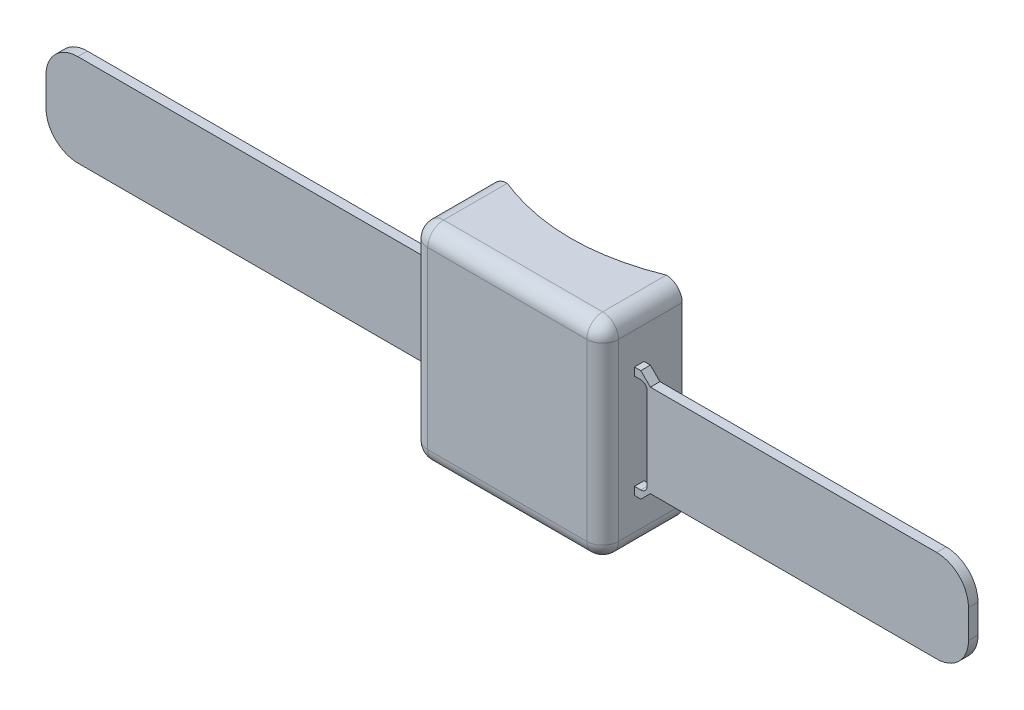
SolidWorks part; units mm, degrees
ref_plane "Alzado" through (0, 0, 0) normal (0, 0, 1) x (1, 0, 0)
ref_plane "Planta" through (0, 0, 0) normal (0, 1, 0) x (1, 0, 0)
ref_plane "Vista lateral" through (0, 0, 0) normal (1, 0, 0) x (0, 0, -1)
sketch "Croquis1" plane through (0, 0, 0) normal (0, 0, 1) x (1, 0, 0)
  line L0 (5, 0) -> (55, 0)
  line L1 (60, 5) -> (60, 60)
  line L2 (55, 65) -> (5, 65)
  line L3 (0, 60) -> (0, 5)
  arc A0 (5, 0) -> (0, 5) centre (5, 5) cw
  arc A1 (5, 65) -> (0, 60) centre (5, 60) ccw
  arc A2 (60, 60) -> (55, 65) centre (55, 60) ccw
  arc A3 (55, 0) -> (60, 5) centre (55, 5) ccw
  point P7 (0, 0)
  point P12 (60, 65)
  point P15 (60, 0)
  dimension "D1" = 65
  dimension "D3" = 5
  dimension "D2" = 60
extrude "Saliente-Extruir1" add sketch "Croquis1" against normal blind 25
fillet "Redondeo1" radius 5 8 edges at (58.5355, 63.5355, 0) (30, 65, 0) (1.4645, 63.5355, 0) (58.5355, 1.4645, 0) (1.4645, 1.4645, 0) (30, 0, 0) (0, 32.5, 0) (60, 32.5, 0)
sketch "Croquis2" plane through (0, 0, 0) normal (0, -1, 0) x (1, 0, 0)
  line L0 (5, -25) -> (55, -25)
  spline S0 degree 2 poles (5, -25) (30, -15) (55, -25) knots 0 0 0 1 1 1
  point P2 (30, -25)
  point P4 (0, 0)
  dimension "D1" = 5
extrude "Cortar-Extruir1" cut sketch "Croquis2" against normal blind 65
sketch "Croquis3" plane through (0, 0, 0) normal (-1, 0, 0) x (0, 0, 1)
  line L0 (-10, 50) -> (-10, 15)
  line L1 (-10, 15) -> (-13, 15)
  line L2 (-13, 15) -> (-13, 50)
  line L3 (-13, 50) -> (-10, 50)
  line L4 (-25, 0) -> (-5, 0) construction
  line L6 (-25, 60) -> (-25, 5) construction
  point P6 (-15, 0)
  dimension "D1" = 35
  dimension "D2" = 3
  dimension "D3" = 15
  dimension "D4" = 12
extrude "Saliente-Extruir2" add sketch "Croquis3" along normal blind 5
sketch "Croquis4" plane through (0, 0, -10) normal (0, 0, 1) x (1, 0, 0)
  line L0 (-2, 47.5) -> (0, 47.5)
  line L1 (0, 15) -> (0, 50) construction
  line L2 (0, 47.5) -> (0, 17.5)
  line L3 (0, 17.5) -> (-2, 17.5)
  line L4 (-4, 19.5) -> (-4, 45.5)
  line L5 (-5, 50) -> (0, 50) construction
  arc A0 (-2, 47.5) -> (-4, 45.5) centre (-2, 45.5) ccw
  arc A1 (-2, 17.5) -> (-4, 19.5) centre (-2, 19.5) cw
  point P5 (-1, 47.5)
  point P11 (-4, 47.5)
  point P14 (-4, 17.5)
  dimension "D4" = 2
  dimension "D1" = 30
  dimension "D2" = 4
  dimension "D3" = 2.5
extrude "Cortar-Extruir2" cut sketch "Croquis4" against normal blind 3
chamfer "Chaflán2" distance 3 angle 45 2 edges at (-5, 50, -11.5) (-5, 15, -11.5)
ref_plane "Plano1" through (30, 0, 0) normal (1, 0, 0) x (0, 0, -1)
mirror "Simetría1" about plane through (30, 0, 0) normal (1, 0, 0) of "Saliente-Extruir2"
mirror "Simetría2" about plane through (30, 0, 0) normal (1, 0, 0) of "Cortar-Extruir2"
chamfer "Chaflán3" distance 3 angle 45 2 edges at (65, 50, -11.5) (65, 15, -11.5)
ref_plane "Plano2" through (0, 0, -19.5) normal (0, 0, 1) x (1, 0, 0)
sketch "Croquis6" plane through (0, 0, -19.5) normal (0, 0, 1) x (1, 0, 0)
  line L0 (30, -13.75) -> (30, 13.75) construction
  circle A0 centre (30, 32.5) radius 9
  dimension "D1" = 18
extrude "Cortar-Extruir5" cut sketch "Croquis6" against normal blind 1.5
sketch "Croquis7" plane through (0, 0, 0) normal (0, -1, 0) x (1, 0, 0)
  line L4 (55, -25) -> (55, -5) construction
  line L5 (26, -9) -> (34, -9)
  line L6 (25, -10) -> (25, -12)
  line L7 (26, -13) -> (34, -13)
  line L8 (35, -10) -> (35, -12)
  line L10 (55, -5) -> (5, -5) construction
  arc A0 (25, -12) -> (26, -13) centre (26, -12) ccw
  arc A1 (26, -9) -> (25, -10) centre (26, -10) ccw
  arc A2 (34, -9) -> (35, -10) centre (34, -10) cw
  arc A3 (34, -13) -> (35, -12) centre (34, -12) ccw
  point P8 (25, -9)
  point P11 (35, -9)
  point P14 (35, -13)
  point P15 (35, -11)
  dimension "D3" = 1
  dimension "D1" = 10
  dimension "D2" = 4
  dimension "D4" = 20
  dimension "D5" = 4
extrude "Cortar-Extruir6" cut sketch "Croquis7" against normal blind 2.5
sketch "Croquis9" plane through (-5, 0, 0) normal (-1, 0, 0) x (0, 0, 1)
  line L0 (-13, 47) -> (-10, 47)
  line L1 (-10, 47) -> (-10, 18)
  line L2 (-10, 18) -> (-13, 18)
  line L3 (-13, 18) -> (-13, 47)
extrude "Saliente-Extruir3" add sketch "Croquis9" along normal blind 120 separate body
sketch "Croquis10" plane through (0, 0, -10) normal (0, 0, 1) x (1, 0, 0)
  line L0 (-5, 47) -> (-115, 47)
  line L1 (-125, 37) -> (-125, 28)
  line L2 (-115, 18) -> (-5, 18)
  line L3 (-5, 18) -> (-5, 47)
  line L4 (-115, 18) -> (-125, 18)
  line L5 (-125, 18) -> (-125, 28)
  line L6 (-125, 47) -> (-115, 47)
  line L7 (-125, 37) -> (-125, 47)
  arc A0 (-115, 47) -> (-125, 37) centre (-115, 37) ccw
  arc A1 (-125, 28) -> (-115, 18) centre (-115, 28) ccw
  point P10 (-125, 47)
  point P13 (-125, 18)
  line M8 (-5, 47) -> (-125, 47)
  line M9 (-125, 47) -> (-125, 18)
  line M10 (-125, 18) -> (-5, 18)
  dimension "D1" = 10
extrude "Cortar-Extruir7" cut sketch "Croquis10" against normal blind 3 contours A0 M8 M9 | A1 M9 M10
sketch "Croquis11" plane through (65, 0, 0) normal (1, 0, 0) x (0, 0, -1)
  line L0 (10, 47) -> (13, 47)
  line L1 (13, 47) -> (13, 18)
  line L2 (13, 18) -> (10, 18)
  line L3 (10, 18) -> (10, 47)
extrude "Saliente-Extruir4" add sketch "Croquis11" along normal blind 100
sketch "Croquis12" plane through (0, 0, -10) normal (0, 0, 1) x (1, 0, 0)
  line L0 (65, 47) -> (155, 47)
  line L1 (165, 37) -> (165, 28)
  line L2 (155, 18) -> (65, 18)
  line L3 (65, 18) -> (65, 47)
  line L4 (155, 18) -> (165, 18)
  line L5 (165, 18) -> (165, 28)
  line L6 (165, 37) -> (165, 47)
  line L7 (165, 47) -> (155, 47)
  arc A0 (155, 47) -> (165, 37) centre (155, 37) cw
  arc A1 (165, 28) -> (155, 18) centre (155, 28) cw
  point P10 (165, 47)
  point P13 (165, 18)
  line M8 (65, 18) -> (165, 18)
  line M9 (165, 18) -> (165, 47)
  line M10 (165, 47) -> (65, 47)
  dimension "D1" = 10
extrude "Cortar-Extruir8" cut sketch "Croquis12" against normal blind 3 contours A1 M9 M8 | A0 M10 M9
